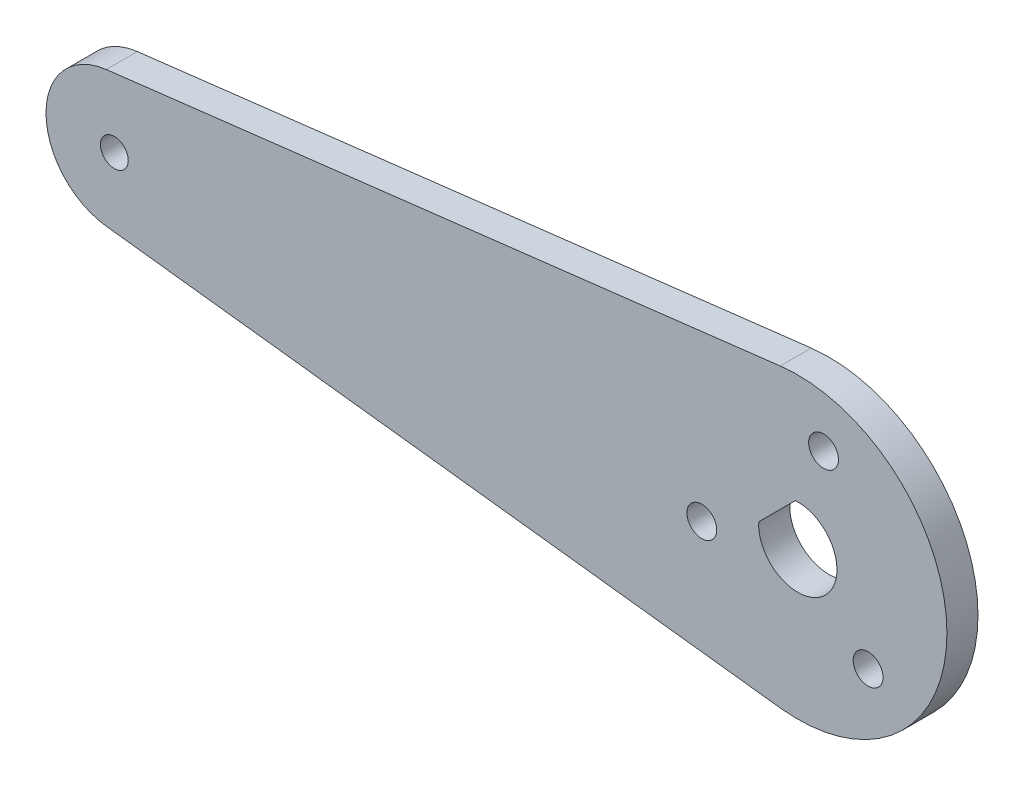
SolidWorks part; units mm, degrees
ref_plane "Front Plane" through (0, 0, 0) normal (0, 0, 1) x (1, 0, 0)
ref_plane "Top Plane" through (0, 0, 0) normal (0, 1, 0) x (1, 0, 0)
ref_plane "Right Plane" through (0, 0, 0) normal (1, 0, 0) x (0, 0, -1)
sketch "Sketch1" plane through (0, 0, 0) normal (0, 0, 1) x (1, 0, 0)
  line L0 (-70.6755, 6.936) -> (-1.8011, 15.1332)
  line L1 (-70.6755, -6.936) -> (-1.8011, -15.1332)
  line L2 (-0.2505, 3.9921) -> (-3.9921, 0.2505)
  line L3 (-2.1213, 2.1213) -> (7.1842, -7.1842) construction
  arc A0 (-70.6755, 6.936) -> (-70.6755, -6.936) centre (-69.85, 0) ccw
  arc A1 (-1.8011, 15.1332) -> (-1.8011, -15.1332) centre (0, 0) cw
  circle A2 centre (-69.85, 0) radius 1.4224
  arc A3 (-0.2505, 3.9921) -> (-3.9921, 0.2505) centre (0, 0) cw
  circle A4 centre (7.1842, -7.1842) radius 1.524
  circle A5 centre (-9.8138, -2.6296) radius 1.524
  circle A6 centre (2.6296, 9.8138) radius 1.524
  dimension "D1" = 2.8448
  dimension "D3" = 6.985
  dimension "D4" = 15.24
  dimension "D5" = 4
  dimension "D7" = 3.048
  dimension "D2" = 69.85
  dimension "D6" = 3
  dimension "D8" = 10.16
  dimension "D9" = 3
extrude "Boss-Extrude1" add sketch "Sketch1" along normal blind 3.175
